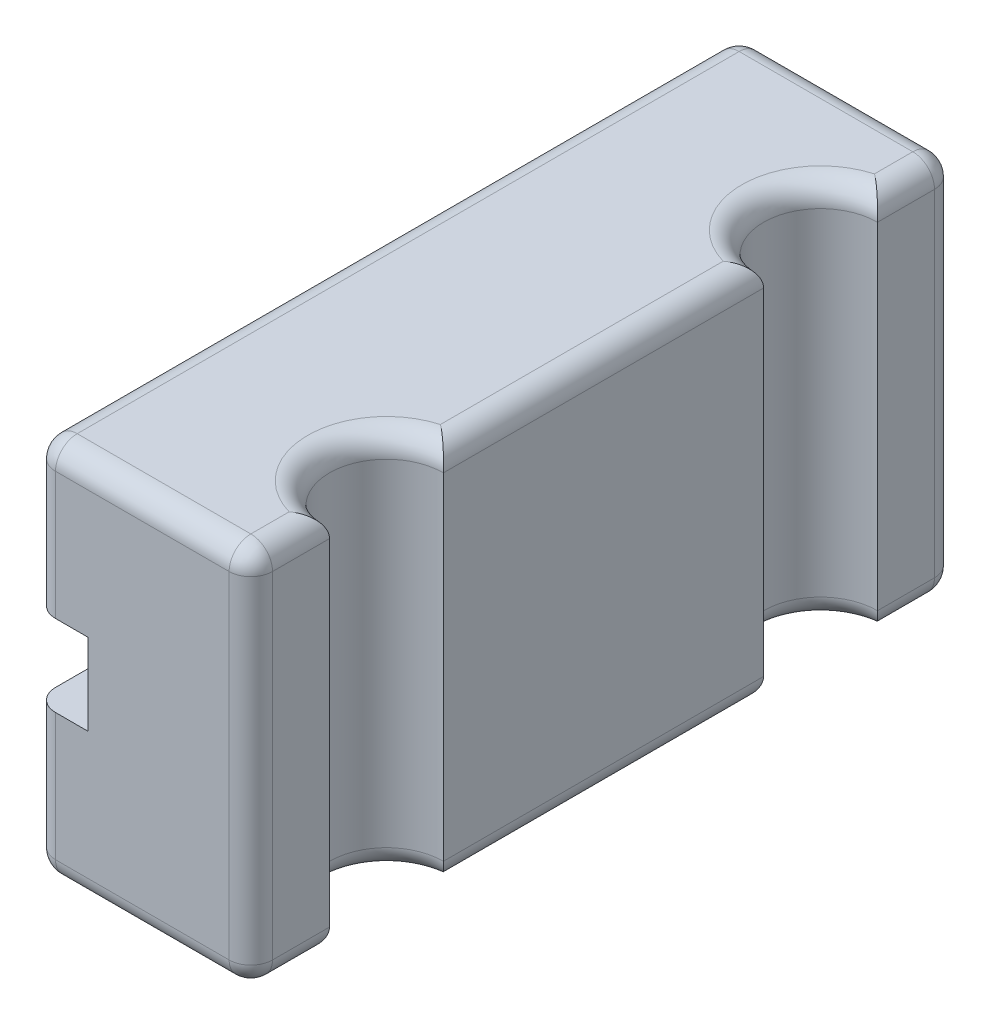
SolidWorks part; units mm, degrees
ref_plane "Front Plane" through (0, 0, 0) normal (0, 0, 1) x (1, 0, 0)
ref_plane "Top Plane" through (0, 0, 0) normal (0, 1, 0) x (1, 0, 0)
ref_plane "Right Plane" through (0, 0, 0) normal (1, 0, 0) x (0, 0, -1)
sketch "Sketch2" plane through (0, 0, 0) normal (0, 1, 0) x (1, 0, 0)
  line L0 (5.25, 14.75) -> (5.25, -14.75)
  line L1 (0, 25.25) -> (50.5, 25.25) construction
  line L2 (0, 25.25) -> (0, -25.25) construction
  line L3 (0, -25.25) -> (50.5, -25.25) construction
  line L4 (50.5, 25.25) -> (50.5, -25.25) construction
  line L5 (0, 25.25) -> (50.5, -25.25) construction
  line L6 (0, -25.25) -> (50.5, 25.25) construction
  line L7 (10.5, -20) -> (40, -20) construction
  line L8 (45.25, -14.75) -> (45.25, 14.75) construction
  line L9 (10.5, 20) -> (40, 20) construction
  line L10 (5.25, 25.25) -> (5.25, 32.5)
  line L11 (5.25, 32.5) -> (-14.75, 32.5)
  line L12 (-14.75, 32.5) -> (-14.75, -32.5)
  line L13 (-14.75, -32.5) -> (5.25, -32.5)
  line L14 (5.25, -32.5) -> (5.25, -25.25)
  arc A0 (5.25, 25.25) -> (5.25, 14.75) centre (5.25, 20) ccw
  arc A1 (5.25, -14.75) -> (5.25, -25.25) centre (5.25, -20) ccw
  circle A2 centre (45.25, -20) radius 5.25 construction
  circle A3 centre (45.25, 20) radius 5.25 construction
  arc A4 (10.5, 20) -> (5.25, 25.25) centre (5.25, 20) ccw construction
  arc A5 (8.9623, 16.2877) -> (10.5, 20) centre (5.25, 20) ccw construction
  arc A6 (5.25, 14.75) -> (8.9623, 16.2877) centre (5.25, 20) ccw construction
  arc A7 (8.9623, -16.2877) -> (5.25, -14.75) centre (5.25, -20) ccw construction
  arc A8 (10.5, -20) -> (8.9623, -16.2877) centre (5.25, -20) ccw construction
  arc A9 (5.25, -25.25) -> (10.5, -20) centre (5.25, -20) ccw construction
  point P0 (25.25, 0)
  point P5 (0, 0)
  dimension "D2" = 10.5
  dimension "D1" = 50.5
  dimension "D3" = 20
  dimension "D4" = 65
extrude "Boss-Extrude1" add sketch "Sketch2" along normal mid plane 35
fillet "Fillet1" radius 2 20 edges at (5.25, 0, -32.5) (-14.75, 0, -32.5) (-14.75, 0, 32.5) (5.25, 0, 32.5) (5.25, -17.5, -28.875) (-4.75, -17.5, -32.5) (-14.75, -17.5, 0) (-4.75, -17.5, 32.5) (5.25, -17.5, 28.875) (0, -17.5, 20) (5.25, -17.5, 0) (0, -17.5, -20) (5.25, 17.5, 0) (0, 17.5, 20) (5.25, 17.5, 28.875) (-4.75, 17.5, 32.5) (-14.75, 17.5, 0) (-4.75, 17.5, -32.5) (5.25, 17.5, -28.875) (0, 17.5, -20)
sketch "Sketch3" plane through (0, 0, 32.5) normal (0, 0, 1) x (1, 0, 0)
  line L0 (-14.75, -15.5) -> (-14.75, 15.5) construction
  line L1 (-9.75, -3.75) -> (-14.75, -3.75)
  line L2 (-9.75, -3.75) -> (-9.75, 3.75)
  line L3 (-9.75, 3.75) -> (-14.75, 3.75)
  line L4 (-14.75, -3.75) -> (-14.75, 3.75)
  line L5 (-9.75, -3.75) -> (-14.75, 3.75) construction
  line L6 (-9.75, 3.75) -> (-14.75, -3.75) construction
  point P0 (-12.25, 0)
  dimension "D1" = 5
  dimension "D2" = 7.5
extrude "Cut-Extrude1" cut sketch "Sketch3" against normal through all
equation "\"∩╗┐cas_w\" = 38.1mm"
equation "\"cas_l\" = 83.0mm"
equation "\"cas_h\" = 280.0mm"
equation "\"rail_w\" = 50.5mm"
equation "\"rail_c\" = 10.5mm"
equation "\"D1@Sketch2\"=\"rail_w\""
equation "\"D2@Sketch2\"=\"rail_c\""
